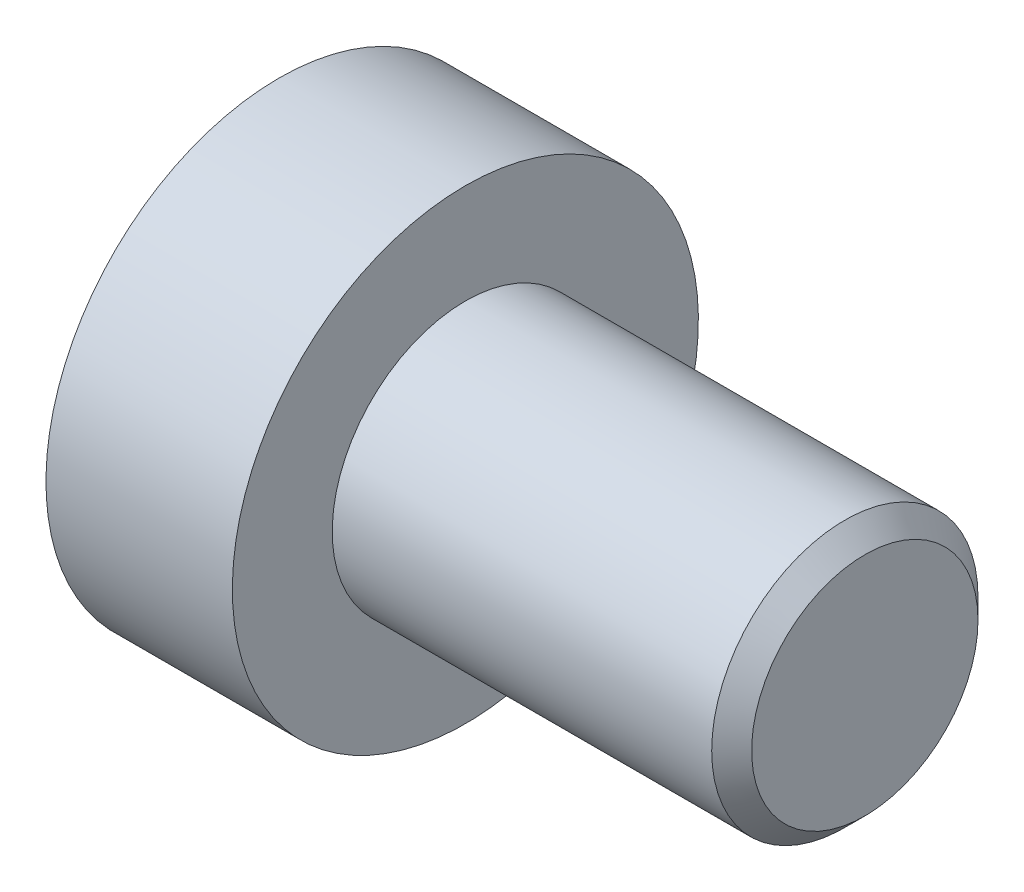
SolidWorks part; units mm, degrees
material "Plain Carbon Steel"
ref_plane "Front Plane" through (0, 0, 0) normal (0, 0, 1) x (1, 0, 0)
ref_plane "Top Plane" through (0, 0, 0) normal (0, 1, 0) x (1, 0, 0)
ref_plane "Right Plane" through (0, 0, 0) normal (1, 0, 0) x (0, 0, -1)
sketch "Sketch2" plane through (0, 0, 0) normal (1, 0, 0) x (0, 0, -1)
  circle A0 centre (0, 0) radius 2
  dimension "D1" = 4
extrude "Boss-Extrude1" add sketch "Sketch2" against normal blind 6
chamfer "Chamfer1" distance 0.3 angle 45 1 edges at (0, 0, -2)
sketch "Sketch6" plane through (0, 0, 0) normal (0, 0, 1) x (1, 0, 0)
  line L0 (-8.8, 0) -> (-8.8, 3.5)
  line L1 (-8.8, 0) -> (-6, 0)
  line L2 (-8.8, 3.5) -> (-6, 3.5)
  line L6 (-6, 3.5) -> (-6, 0)
  line L8 (-6, 0) -> (-14.6471, 0) construction
  line L10 (-6, 2) -> (-6, -2) construction
  dimension "D1" = 2.8
  dimension "D2" = 7
revolve "Revolve1" add sketch "Sketch6" angle 360 about L8
sketch "Sketch7" plane through (-8.8, 0, 0) normal (-1, 0, 0) x (0, 0, 1)
  line L1 (0, 1.4434) -> (-1.25, 0.7217)
  line L2 (-1.25, 0.7217) -> (-1.25, -0.7217)
  line L3 (-1.25, -0.7217) -> (0, -1.4434)
  line L4 (0, -1.4434) -> (1.25, -0.7217)
  line L5 (1.25, -0.7217) -> (1.25, 0.7217)
  line L6 (1.25, 0.7217) -> (0, 1.4434)
  circle A0 centre (0, 0) radius 1.25 construction
  dimension "D1" = 2.5
extrude "Cut-Extrude1" cut sketch "Sketch7" against normal blind 1.6
sketch "Sketch8" plane through (-8.8, 0, 0) normal (-1, 0, 0) x (0, 0, 1)
  circle A0 centre (0, 0) radius 1.4934
  dimension "D1" = 0.05
extrude "Cut-Extrude2" cut sketch "Sketch8" against normal blind 1 draft 45
